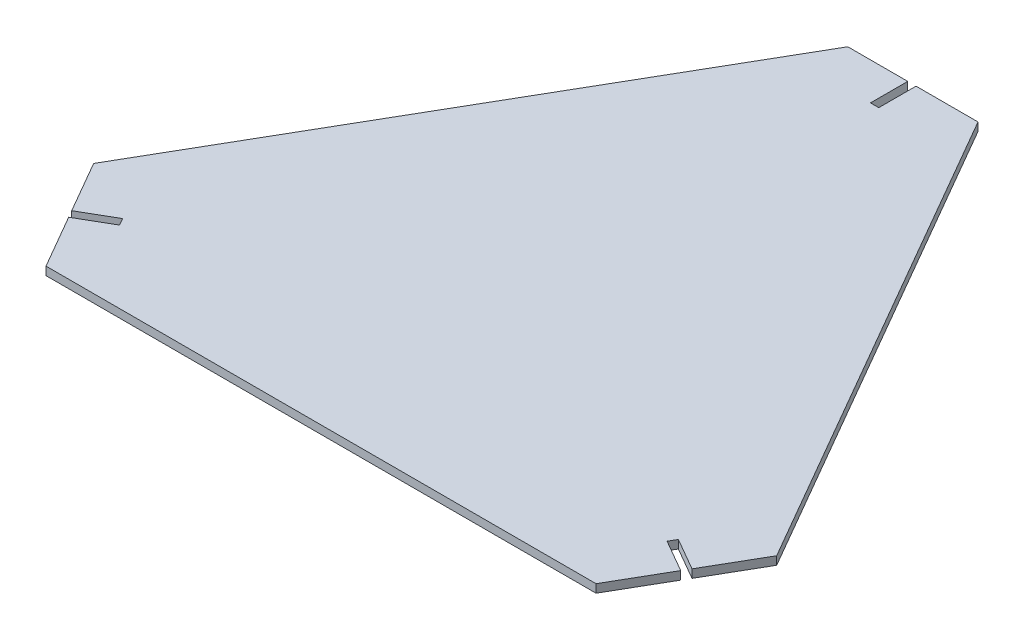
SolidWorks part; units mm, degrees
material "Haya"
ref_plane "Alzado" through (0, 0, 0) normal (0, 0, 1) x (1, 0, 0)
ref_plane "Planta" through (0, 0, 0) normal (0, 1, 0) x (1, 0, 0)
ref_plane "Vista lateral" through (0, 0, 0) normal (1, 0, 0) x (0, 0, -1)
sketch "Croquis1" plane through (0, 0, 0) normal (0, 1, 0) x (1, 0, 0)
  line L0 (-129.9038, -55) -> (-17.3205, 140)
  line L1 (17.3205, 140) -> (129.9038, -55)
  line L2 (112.5833, -85) -> (-112.5833, -85)
  line L3 (0, 0) -> (0, -85) construction
  line L4 (-73.6122, 42.5) -> (0, 0) construction
  line L5 (0, 0) -> (73.6122, 42.5) construction
  arc A0 (-129.9038, -55) -> (-112.5833, -85) centre (-112.5833, -65) ccw
  arc A1 (129.9038, -55) -> (112.5833, -85) centre (112.5833, -65) cw
  arc A2 (-17.3205, 140) -> (17.3205, 140) centre (0, 130) cw
  point P9 (0, -60)
  dimension "D3" = 20
  dimension "D1" = 25
  dimension "D2" = 60
extrude "Saliente-Extruir1" add sketch "Croquis1" along normal mid plane 3
sketch "Croquis2" plane through (0, 1.5, 0) normal (0, 1, 0) x (1, 0, 0)
  line L0 (129.9038, -75) -> (95.2628, -55) construction
  line L1 (122.5833, -47.6795) -> (102.5833, -82.3205) construction
  line L2 (107.5032, -63.799) -> (109.0032, -61.201)
  line L3 (109.0032, -61.201) -> (100.3429, -56.201)
  line L4 (100.3429, -56.201) -> (98.8429, -58.799)
  line L5 (98.8429, -58.799) -> (107.5032, -63.799)
  line L6 (113.7843, -59.9199) -> (116.3823, -61.4199)
  line L7 (116.3823, -61.4199) -> (121.3823, -52.7596)
  line L8 (118.7843, -51.2596) -> (113.7843, -59.9199)
  line L9 (121.3823, -52.7596) -> (118.7843, -51.2596)
  line L10 (117.6634, -66.201) -> (116.1634, -68.799)
  line L11 (116.1634, -68.799) -> (124.8237, -73.799)
  line L12 (126.3237, -71.201) -> (117.6634, -66.201)
  line L13 (124.8237, -73.799) -> (126.3237, -71.201)
  line L14 (111.3823, -70.0801) -> (108.7843, -68.5801)
  line L15 (108.7843, -68.5801) -> (103.7843, -77.2404)
  line L16 (106.3823, -78.7404) -> (111.3823, -70.0801)
  line L17 (103.7843, -77.2404) -> (106.3823, -78.7404)
  circle A0 centre (112.5833, -65) radius 20 construction
  arc A1 (112.5833, -85) -> (129.9038, -55) centre (112.5833, -65) ccw construction
  point P13 (108.2532, -62.5)
  point P30 (112.5833, -65)
  dimension "D1" = 3
  dimension "D2" = 10
  dimension "D3" = 5
  dimension "D4" = 4
extrude "Cortar-Extruir1" cut sketch "Croquis2" against normal up to next (3 mm away)
pattern_circular "MatrizC1" count 3 every 120 about axis through (-0.3691, 0, -0.2131) along (0, 1, 0) of "Cortar-Extruir1"
sketch "Croquis3" [suppressed] plane through (0, 1.5, 0) normal (0, 1, 0) x (1, 0, 0)
  line L0 (22, -75) -> (52, -75) construction
  line L1 (22, -72.9) -> (52, -72.9)
  line L2 (22, -77.1) -> (52, -77.1)
  line L3 (-112.5833, -85) -> (112.5833, -85) construction
  line L4 (22, -45) -> (52, -45) construction
  line L5 (22, -42.9) -> (52, -42.9)
  line L6 (22, -47.1) -> (52, -47.1)
  arc A0 (22, -72.9) -> (22, -77.1) centre (22, -75) ccw
  arc A1 (52, -77.1) -> (52, -72.9) centre (52, -75) ccw
  arc A2 (22, -42.9) -> (22, -47.1) centre (22, -45) ccw
  arc A3 (52, -47.1) -> (52, -42.9) centre (52, -45) ccw
  point P2 (37, -75)
  point P12 (37, -45)
  dimension "D3" = 2.1
  dimension "D1" = 22
  dimension "D2" = 10
  dimension "D4" = 30
  dimension "D5" = 25.8
extrude "Cortar-Extruir2" [suppressed] cut sketch "Croquis3" against normal up to next
pattern_circular "MatrizC2" [suppressed] count 3 every 120
sketch "Croquis4" [suppressed] plane through (0, 1.5, 0) normal (0, 1, 0) x (1, 0, 0)
  line L0 (0, -85) -> (0, -35) construction
  line L1 (-112.5833, -85) -> (112.5833, -85) construction
  line L2 (-4, -85) -> (-4, -35)
  line L3 (4, -85) -> (4, -35)
  line L4 (-4, -85) -> (4, -85)
  arc A1 (4, -35) -> (-4, -35) centre (0, -35) ccw
  point P5 (0, -65.3098)
  dimension "D1" = 8
  dimension "D2" = 50
extrude "Cortar-Extruir3" [suppressed] cut sketch "Croquis4" against normal up to next
pattern_circular "MatrizC3" [suppressed] count 3 every 120
sketch "Croquis5" plane through (0, 1.5, 0) normal (0, 1, 0) x (1, 0, 0)
  line L0 (-123.6334, -44.1393) -> (-112.7725, -62.951)
  line L1 (-17.3205, 140) -> (-129.9038, -55) construction
  line L2 (-112.7725, -62.951) -> (-109.7414, -61.201)
  line L3 (-109.7414, -61.201) -> (-108.2414, -63.799)
  line L4 (-108.2414, -63.799) -> (-111.2725, -65.549)
  line L5 (-111.2725, -65.549) -> (-100.0425, -85)
  line L6 (-112.5833, -85) -> (112.5833, -85) construction
  line L7 (-114.5225, -59.9199) -> (-119.5225, -51.2596) construction
  line L8 (-101.0812, -56.201) -> (-109.7414, -61.201) construction
  line L9 (-108.2414, -63.799) -> (-99.5812, -58.799) construction
  line L10 (-109.7414, -61.201) -> (-108.2414, -63.799) construction
  line L11 (-123.6334, -44.1393) -> (-147.2243, -85)
  line L12 (-147.2243, -85) -> (-100.0425, -85)
  line L13 (-1.8691, 129.1393) -> (-23.5909, 129.1393)
  line L14 (23.5909, 129.1393) -> (1.1309, 129.1393)
  line L15 (23.5909, 129.1393) -> (0, 170)
  line L16 (0, 170) -> (-23.5909, 129.1393)
  line L17 (1.1309, 129.1393) -> (1.1309, 125.6393)
  line L18 (-1.8691, 125.6393) -> (-1.8691, 129.1393)
  line L19 (1.1309, 125.6393) -> (-1.8691, 125.6393)
  line L20 (112.0343, -62.951) -> (123.2643, -43.5)
  line L21 (99.3042, -85) -> (110.5343, -65.549)
  line L22 (99.3042, -85) -> (147.2243, -85)
  line L23 (147.2243, -85) -> (123.2643, -43.5)
  line L24 (110.5343, -65.549) -> (107.5032, -63.799)
  line L25 (109.0032, -61.201) -> (112.0343, -62.951)
  line L26 (107.5032, -63.799) -> (109.0032, -61.201)
  line L28 (-1.8691, 125.6393) -> (-1.8691, 115.6393) construction
  line L29 (1.1309, 115.6393) -> (1.1309, 125.6393) construction
  line L30 (-15.3691, 129.1393) -> (-5.3691, 129.1393) construction
  line L31 (129.9038, -55) -> (17.3205, 140) construction
  line L32 (1.1309, 125.6393) -> (-1.8691, 125.6393) construction
  line L33 (109.0032, -61.201) -> (100.3429, -56.201) construction
  line L36 (108.7843, -68.5801) -> (103.7843, -77.2404) construction
  line L37 (98.8429, -58.799) -> (107.5032, -63.799) construction
  point P37 (0, 0)
extrude "Cortar-Extruir4" cut sketch "Croquis5" against normal up to next
equation "\"DMs\"=60"
equation "\"D2@Croquis1\"=\"DMs\""
equation "\"R\"=20"
equation "\"D3@Croquis1\"=\"R\""
equation "\"G\"= 3"
equation "\"D1@Saliente-Extruir1\"=\"G\""
equation "\"D1@Croquis2\"=\"G\""
equation "\"LE\"=10"
equation "\"D2@Croquis2\"=\"LE\""
equation "\"RiP\"=5"
equation "\"D3@Croquis2\"=\"RiP\""
equation "\"D1@Croquis4\"=8"
equation "\"C\"=50"
equation "\"D2@Croquis4\"=\"C\""
